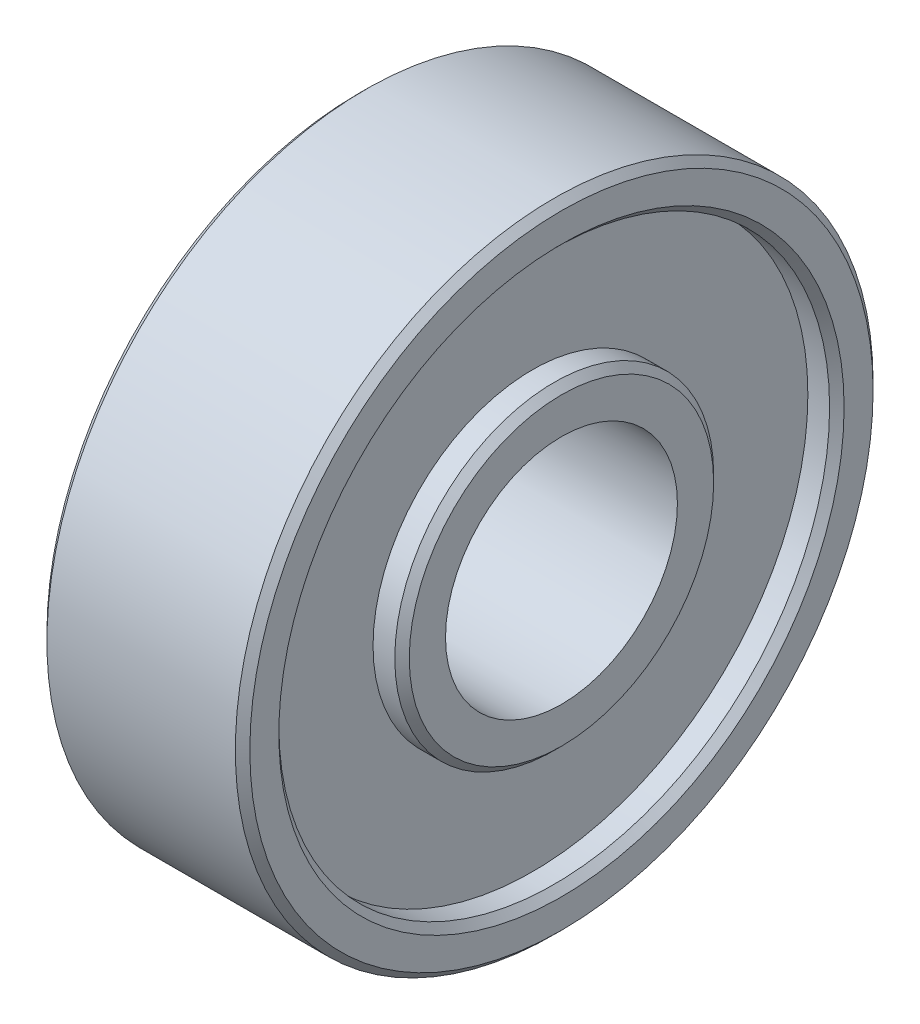
SolidWorks part; units mm, degrees
material "Chrome Stainless Steel"
ref_plane "Front" through (0, 0, 0) normal (0, 0, 1) x (1, 0, 0)
ref_plane "Top" through (0, 0, 0) normal (0, 1, 0) x (1, 0, 0)
ref_plane "Right" through (0, 0, 0) normal (1, 0, 0) x (0, 0, -1)
sketch "Sketch1" plane through (0, 0, 0) normal (1, 0, 0) x (0, 0, -1)
  circle A0 centre (0, 0) radius 11
  circle A1 centre (0, 0) radius 4
extrude "Extrude1" add sketch "Sketch1" along normal blind 7
chamfer "Chamfer1" distance 0.25 angle 45 3 edges at (0, 0, -11) (7, 0, -11) (0, 0, -4)
sketch "Sketch2" plane through (0, 0, 0) normal (-1, 0, 0) x (0, 0, 1)
  circle A0 centre (0, 0) radius 5.5
  circle A1 centre (0, 0) radius 9.5
extrude "Cut-Extrude1" cut sketch "Sketch2" against normal blind 1
sketch "Sketch3" plane through (7, 0, 0) normal (1, 0, 0) x (0, 0, -1)
  circle A0 centre (0, 0) radius 5.5
  circle A1 centre (0, 0) radius 9.5
extrude "Cut-Extrude2" cut sketch "Sketch3" against normal blind 1
chamfer "Chamfer2" distance 0.25 angle 45 4 edges at (0, 0, 5.5) (0, 0, 9.5) (7, 0, -5.5) (7, 0, -9.5)
